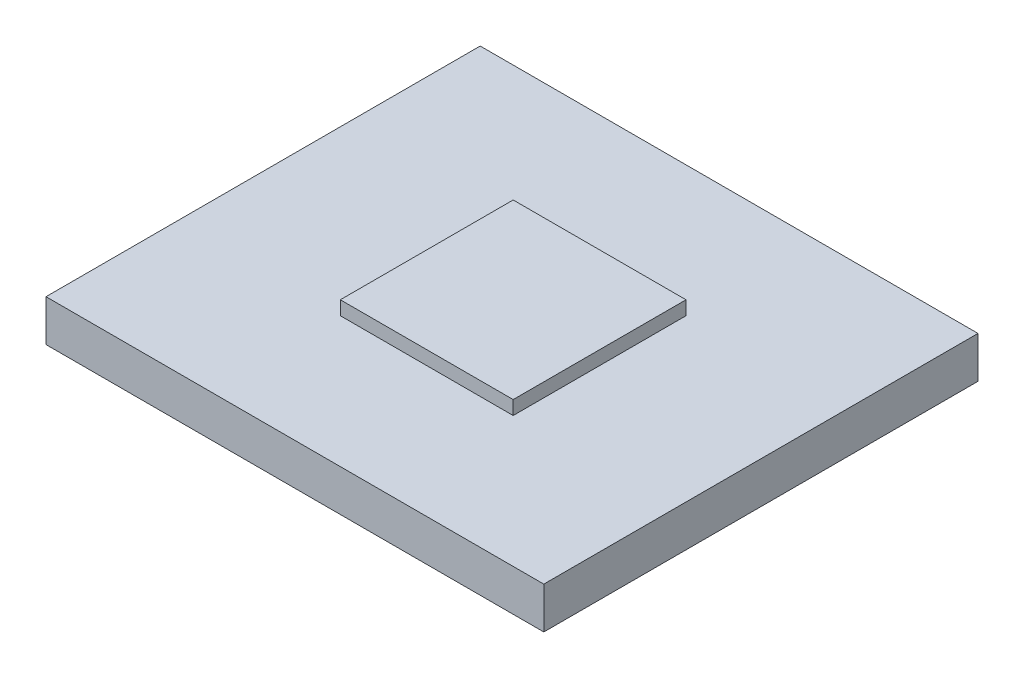
SolidWorks part; units mm, degrees
ref_plane "Alzado" through (0, 0, 0) normal (0, 0, 1) x (1, 0, 0)
ref_plane "Planta" through (0, 0, 0) normal (0, 1, 0) x (1, 0, 0)
ref_plane "Vista lateral" through (0, 0, 0) normal (1, 0, 0) x (0, 0, -1)
sketch "Croquis1" plane through (0, 0, 0) normal (0, -1, 0) x (1, 0, 0)
  line L0 (0, 7.85) -> (0, -7.85)
  line L1 (0, -7.85) -> (18, -7.85)
  line L2 (18, -7.85) -> (18, 7.85)
  line L4 (18, 7.85) -> (0, 7.85)
  point P8 (0, 0)
  point P9 (0, 0)
  point P10 (0, 0)
  point P11 (0, 0)
  dimension "D1" = 15.7
  dimension "D2" = 18
extrude "Saliente-Extruir1" add sketch "Croquis1" along normal blind 1.5
sketch "Croquis2" plane through (0, 0, 0) normal (0, 1, 0) x (1, 0, 0)
  line L0 (5.9177, 3.125) -> (12.1677, 3.125)
  line L1 (12.1677, 3.125) -> (12.1677, -3.125)
  line L2 (12.1677, -3.125) -> (5.9177, -3.125)
  line L3 (5.9177, -3.125) -> (5.9177, 3.125)
  line L4 (9, 7.85) -> (9, -7.85) construction
  line L5 (0, 7.85) -> (18, 7.85) construction
  line L6 (18, -7.85) -> (0, -7.85) construction
  line L7 (0, 0) -> (18, 0) construction
  line L8 (18, 7.85) -> (18, -7.85) construction
  line L9 (5.9177, 0) -> (12.1677, 0) construction
  line L10 (9.0427, 3.125) -> (9.0427, -3.125) construction
  dimension "D1" = 6.25
  dimension "D2" = 6.25
extrude "Saliente-Extruir2" add sketch "Croquis2" along normal blind 0.5
